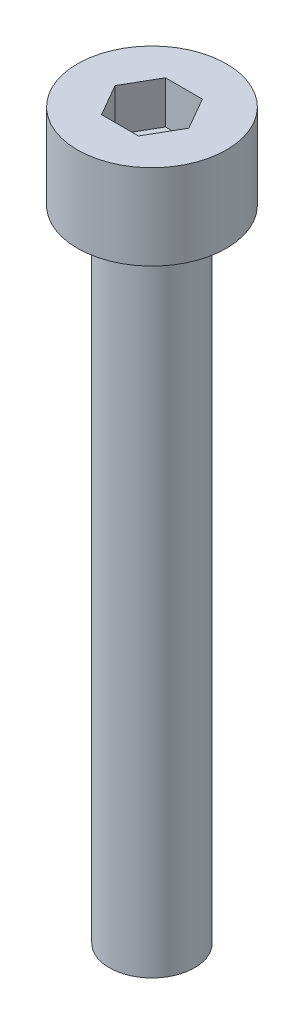
SolidWorks part; units mm, degrees
material "AISI 304"
ref_plane "前视基准面" through (0, 0, 0) normal (0, 0, 1) x (1, 0, 0)
ref_plane "上视基准面" through (0, 0, 0) normal (0, 1, 0) x (1, 0, 0)
ref_plane "右视基准面" through (0, 0, 0) normal (1, 0, 0) x (0, 0, -1)
sketch "草图1" plane through (0, 0, 0) normal (0, 1, 0) x (1, 0, 0)
  circle A0 centre (0, 0) radius 3.5
  dimension "D1" = 7
extrude "杯头" add sketch "草图1" along normal blind 4
sketch "草图2" plane through (0, 4, 0) normal (0, 1, 0) x (1, 0, 0)
  line L1 (1.7321, 0) -> (0.866, 1.5)
  line L2 (0.866, 1.5) -> (-0.866, 1.5)
  line L3 (-0.866, 1.5) -> (-1.7321, 0)
  line L4 (-1.7321, 0) -> (-0.866, -1.5)
  line L5 (-0.866, -1.5) -> (0.866, -1.5)
  line L6 (0.866, -1.5) -> (1.7321, 0)
  circle A0 centre (0, 0) radius 1.5 construction
  dimension "D1" = 3
extrude "内六角口" cut sketch "草图2" against normal blind 2
sketch "草图3" plane through (0, 0, 0) normal (0, -1, 0) x (1, 0, 0)
  circle A0 centre (0, 0) radius 2
  dimension "D1" = 4
extrude "螺纹长度" add sketch "草图3" along normal blind 30
